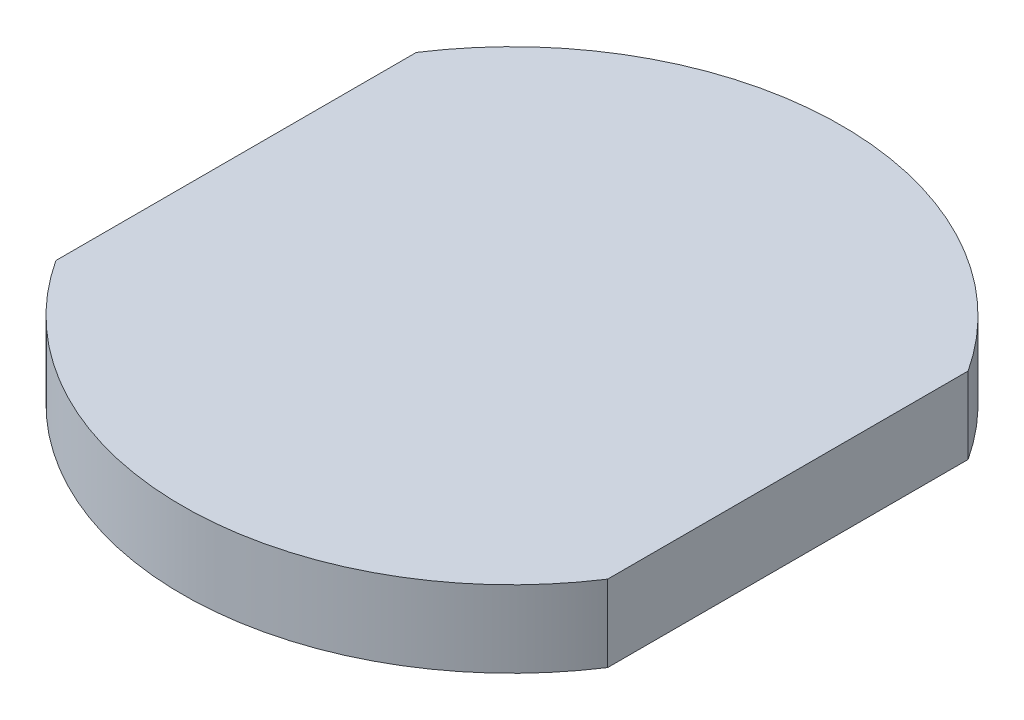
SolidWorks part; units mm, degrees
ref_plane "Ön Düzlem" through (0, 0, 0) normal (0, 0, 1) x (1, 0, 0)
ref_plane "Üst Düzlem" through (0, 0, 0) normal (0, 1, 0) x (1, 0, 0)
ref_plane "Sağ Düzlem" through (0, 0, 0) normal (1, 0, 0) x (0, 0, -1)
sketch "Çizim1" plane through (0, 0, 0) normal (0, 1, 0) x (1, 0, 0)
  line L2 (-18, -11.758) -> (-18, 11.758)
  line L4 (18, -11.758) -> (18, 11.758)
  arc A0 (-18, -11.758) -> (18, -11.758) centre (0, 0) ccw
  arc A1 (18, 11.758) -> (-18, 11.758) centre (0, 0) ccw
  point P0 (0, 0)
  dimension "D3" = 43
  dimension "D1" = 36
extrude "Yükseklik-Ekstrüzyon1" add sketch "Çizim1" against normal blind 5
